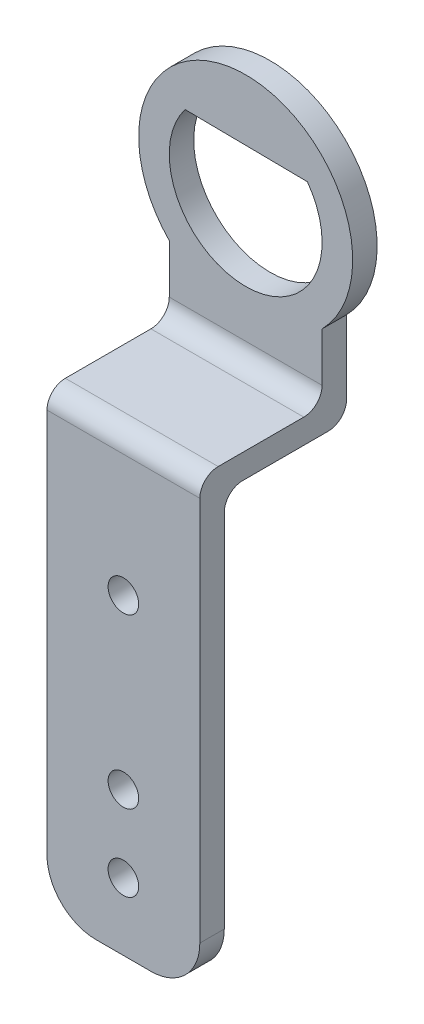
SolidWorks part; units mm, degrees
ref_plane "Front Plane" through (0, 0, 0) normal (0, 0, 1) x (1, 0, 0)
ref_plane "Top Plane" through (0, 0, 0) normal (0, 1, 0) x (1, 0, 0)
ref_plane "Right Plane" through (0, 0, 0) normal (1, 0, 0) x (0, 0, -1)
sketch "Sketch1" plane through (0, 0, 0) normal (0, 0, 1) x (1, 0, 0)
  line L0 (2.5247, -0.0562) -> (0.5248, -0.0329)
  line L3 (0.266, -2.0193) -> (0.266, -3.5193)
  line L4 (0.266, -3.5193) -> (2.766, -3.5193)
  line L5 (2.766, -2.0193) -> (2.766, -3.5193)
  arc A0 (0.5248, -0.0329) -> (2.5247, -0.0562) centre (1.516, -0.7945) ccw
  arc A1 (2.766, -2.0193) -> (0.266, -2.0193) centre (1.516, -0.7945) ccw
  point P9 (0, 0)
  point P10 (0, 0)
  dimension "D1" = 3.5
  dimension "D2" = 1.25
  dimension "D3" = 2.5
  dimension "D4" = 1.5
extrude "Boss-Extrude1" add sketch "Sketch1" along normal blind 0.4
sketch "Sketch2" plane through (0, 0, 0.4) normal (0, 0, 1) x (1, 0, 0)
  line L0 (0.266, -2.0193) -> (0.266, -3.5193) construction
  line L1 (2.766, -3.5193) -> (2.766, -2.0193) construction
  line L2 (0.266, -3.5193) -> (2.766, -3.5193) construction
  line L3 (0.266, -3.1193) -> (0.266, -3.5193)
  line L4 (2.766, -3.5193) -> (2.766, -3.1193)
  line L5 (0.266, -3.5193) -> (2.766, -3.5193)
  line L6 (0.266, -3.1193) -> (2.766, -3.1193)
  dimension "D1" = 0.4
extrude "Boss-Extrude2" add sketch "Sketch2" along normal blind 2
sketch "Sketch3" plane through (0, -3.5193, 0) normal (0, -1, 0) x (1, 0, 0)
  line L0 (0.266, 2.4) -> (0.266, 0) construction
  line L1 (0.266, 2.4) -> (2.766, 2.4) construction
  line L2 (2.766, 2.4) -> (2.766, 0) construction
  line L3 (0.266, 2.4) -> (0.266, 2)
  line L4 (0.266, 2.4) -> (2.766, 2.4)
  line L5 (2.766, 2.4) -> (2.766, 2)
  line L6 (2.766, 2) -> (0.266, 2)
  dimension "D1" = 0.4
extrude "Boss-Extrude3" add sketch "Sketch3" along normal blind 7
fillet "Fillet1" radius 0.3 4 edges at (1.516, -3.1193, 0.4) (1.516, -3.5193, 0) (1.516, -3.5193, 2) (1.516, -3.1193, 2.4)
fillet "Fillet2" radius 0.8 2 edges at (0.266, -10.5193, 2.2) (2.766, -10.5193, 2.2)
sketch "Sketch4" plane through (0, 0, 2.4) normal (0, 0, 1) x (1, 0, 0)
  line L0 (1.516, -3.4193) -> (1.516, -11.4193) construction
  line L1 (2.766, -3.4193) -> (0.266, -3.4193) construction
  line L2 (1.516, -7.4193) -> (2.766, -7.4193) construction
  line L3 (2.766, -9.7193) -> (2.766, -3.4193) construction
  circle A0 centre (1.516, -5.4193) radius 0.25
  circle A1 centre (1.516, -9.4193) radius 0.25
  circle A2 centre (1.516, -8.1693) radius 0.25
  point P12 (0, 0)
  dimension "D1" = 0.5
  dimension "D4" = 0.5
  dimension "D2" = 4
  dimension "D3" = 2
  dimension "D5" = 1.25
extrude "Cut-Extrude1" cut sketch "Sketch4" against normal blind 4
